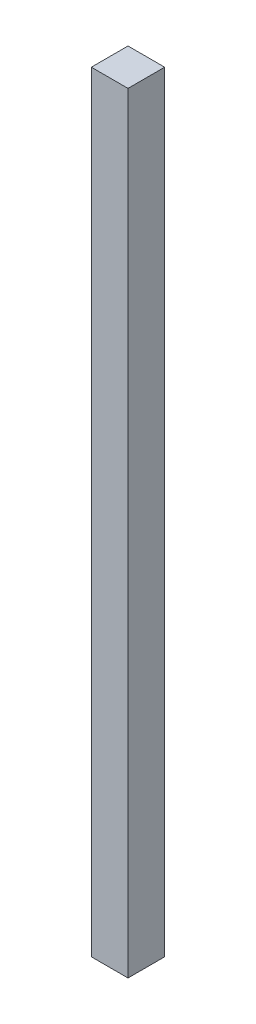
SolidWorks part; units mm, degrees
ref_plane "Front Plane" through (0, 0, 0) normal (0, 0, 1) x (1, 0, 0)
ref_plane "Top Plane" through (0, 0, 0) normal (0, 1, 0) x (1, 0, 0)
ref_plane "Right Plane" through (0, 0, 0) normal (1, 0, 0) x (0, 0, -1)
sketch "Sketch1" plane through (0, 0, 0) normal (0, 1, 0) x (1, 0, 0)
  line L1 (7.5, 7.5) -> (-7.5, 7.5)
  line L2 (7.5, 7.5) -> (7.5, -7.5)
  line L3 (7.5, -7.5) -> (-7.5, -7.5)
  line L4 (-7.5, 7.5) -> (-7.5, -7.5)
  line L5 (7.5, 7.5) -> (-7.5, -7.5) construction
  line L6 (7.5, -7.5) -> (-7.5, 7.5) construction
  point P0 (0, 0)
  dimension "D1" = 15
  dimension "D2" = 15
extrude "Boss-Extrude1" add sketch "Sketch1" along normal blind 315
